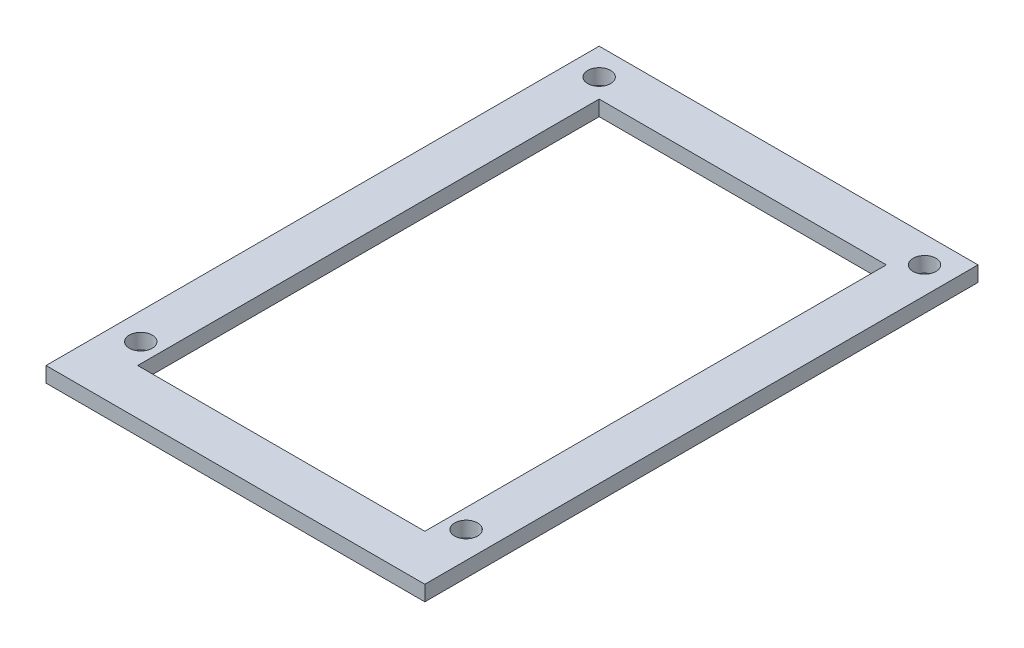
SolidWorks part; units mm, degrees
ref_plane "Front Plane" through (0, 0, 0) normal (0, 0, 1) x (1, 0, 0)
ref_plane "Top Plane" through (0, 0, 0) normal (0, 1, 0) x (1, 0, 0)
ref_plane "Right Plane" through (0, 0, 0) normal (1, 0, 0) x (0, 0, -1)
sketch "Sketch1" plane through (0, 0, 0) normal (0, 1, 0) x (1, 0, 0)
  line L0 (0, 54.6923) -> (0, 7.0673)
  line L1 (39.3591, 54.6923) -> (39.3591, 7.0673)
  line L2 (0, 7.0673) -> (0, 0)
  line L3 (0, 0) -> (39.3591, 0)
  line L4 (39.3591, 7.0673) -> (39.3591, 0)
  line L5 (0, 54.6923) -> (0, 57.4704)
  line L6 (0, 57.4704) -> (39.3591, 57.4704)
  line L7 (39.3591, 57.4704) -> (39.3591, 54.6923)
  line L8 (4.7625, 52.7079) -> (4.7625, 7.0673)
  line L9 (4.7625, 7.0673) -> (4.7625, 4.7625)
  line L10 (4.7625, 4.7625) -> (34.5966, 4.7625)
  line L11 (34.5966, 7.0673) -> (34.5966, 4.7625)
  line L12 (34.5966, 52.7079) -> (34.5966, 7.0673)
  line L13 (4.7625, 52.7079) -> (34.5966, 52.7079)
  circle A0 centre (2.7781, 54.6923) radius 1.1906
  circle A1 centre (36.581, 7.0673) radius 1.1906
  circle A2 centre (2.7781, 7.0673) radius 1.1906
  circle A3 centre (36.581, 54.6923) radius 1.1906
extrude "Boss-Extrude1" add sketch "Sketch1" along normal blind 1.5875
